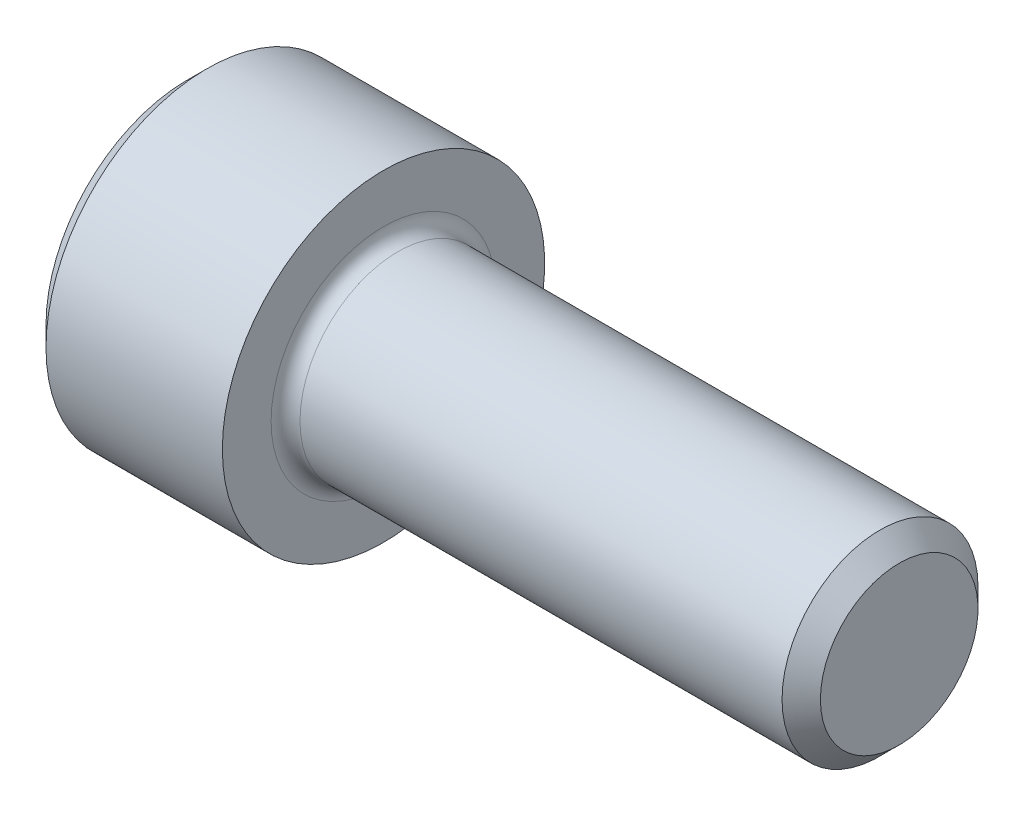
SolidWorks part; units mm, degrees
revolve "Base-Revolve" add sketch "BodySke" angle 360 about L6
sketch "BodySke" plane through (0, 0, 0) normal (0, 0, 1) x (1, 0, 0)
  line L0 (0, 0) -> (0, 3.4861)
  line L1 (0.4826, 3.9687) -> (4.826, 3.9687)
  line L2 (4.826, 3.9687) -> (4.826, 2.413)
  line L3 (4.826, 2.413) -> (17.0536, 2.413)
  line L4 (17.526, 1.9406) -> (17.526, 0)
  line L5 (17.526, 0) -> (0, 0)
  line L6 (-31.75, 0) -> (127, 0) construction
  line L7 (0, 3.4861) -> (0.4826, 3.9687)
  line L8 (17.526, 1.9406) -> (17.0536, 2.413)
  line L9 (0, -3.4862) -> (0.4826, -3.9688) construction
  line L10 (17.526, -1.9406) -> (17.0536, -2.413) construction
  line L11 (5.6185, 9.525) -> (5.6185, 3.175) construction
  line L12 (4.826, 9.525) -> (4.826, 3.175) construction
  line L13 (-20.574, 9.525) -> (-20.574, 3.175) construction
  dimension "Diameter" = 4.826
  dimension "Head_ht" = 4.826
  dimension "Length" = 12.7
  dimension "Body_ch_ang" = 45
  dimension "Head_dia" = 7.9375
  dimension "Head_ch_ang" = 45
  dimension "Head_side_ht" = 4.3434
  dimension "Minor_dia" = 3.8811
  dimension "Advance" = 0.7925
  dimension "Thread_nom" = 12.7
  dimension "Thread_length" = 38.1
cosmetic thread "ThreadCosmetic" parameters "Thread_length"=11.9075, "Thread_minor"=3.8811
material "Alloy Steel"
ref_plane "Plane1" through (0, 0, 0) normal (0, 0, 1) x (1, 0, 0)
ref_plane "Plane2" through (0, 0, 0) normal (0, 1, 0) x (1, 0, 0)
ref_plane "Plane3" through (0, 0, 0) normal (1, 0, 0) x (0, 0, -1)
fillet "Fillet1" radius 0.3556 1 edges at (4.826, 0, 2.413)
sketch "Sketch2" plane through (0, 0, 0) normal (0, 0, 1) x (1, 0, 0)
  line L0 (0, 1.985) -> (2.286, 1.985)
  line L1 (2.286, 1.985) -> (3.432, 0)
  line L2 (-31.75, 0) -> (127, 0) construction
  line L3 (3.432, 0) -> (0, 0)
  line L4 (0, 0) -> (0, 1.985)
  line L5 (0, 3.4861) -> (0, -3.4861) construction
  line L6 (0, 0) -> (47.625, 0) construction
  line L7 (4.826, -3.9687) -> (4.826, 3.9687) construction
  dimension "D1" = 1.985
  dimension "D2" = 60
revolve "Hex-PreBroach" cut sketch "Sketch2" angle 360 about L6
sketch "Sketch3" plane through (0, 0, 0) normal (-1, 0, 0) x (0, 0.5, 0.866)
  line L0 (1.146, 1.985) -> (-1.146, 1.985)
  line L1 (-1.146, 1.985) -> (-2.2921, 0)
  line L2 (1.146, 1.985) -> (2.2921, 0)
  line L3 (1.146, -1.985) -> (2.2921, 0)
  line L4 (1.146, -1.985) -> (-1.146, -1.985)
  line L5 (-1.146, -1.985) -> (-2.2921, 0)
  dimension "D1" = 1.985
  dimension "D2" = 1.985
  dimension "Hex_size" = 3.97
extrude "Hex" cut sketch "Sketch3" against normal blind 2.286
sketch "Sketch4" plane through (0, 0, 0) normal (-1, 0, 0) x (0, 0, 1)
  line L0 (0, 0) -> (2.3876, 0)
  line L1 (0, 0) -> (6.1484, 3.5498) construction
  line L2 (0, 0) -> (1.1938, 2.0677)
  line L3 (1.9883, 0.576) -> (2.2704, 0.7389)
  line L4 (1.493, 1.4339) -> (1.7751, 1.5968)
  arc A0 (1.9883, 0.576) -> (1.493, 1.4339) centre (0, 0) ccw
  arc A1 (2.3876, 0) -> (2.2704, 0.7389) centre (0, 0) ccw
  arc A2 (1.1938, 2.0677) -> (1.7751, 1.5968) centre (0, 0) cw
  dimension "D1" = 30
  dimension "D2" = 60
  dimension "Spline_p_dim" = 0.9906
  dimension "D3" = 0.4953
extrude "Spline" [suppressed] cut sketch "Sketch4" against normal blind 2.286
pattern_circular "CirPattern1" [suppressed] count 6 every 60 about axis through (-31.75, 0, 0) along (1, 0, 0)
sketch "Sketch5" plane through (0, 0, 0) normal (0, 0, 1) x (1, 0, 0)
  line L0 (-31.75, 0) -> (127, 0) construction
  line L2 (0, 3.4861) -> (0, -3.4861) construction
  circle A0 centre (1.651, 0) radius 0.5905
  dimension "Drilled_hole_dia" = 1.1811
  dimension "Drilled_hole_loc" = 1.651
extrude "Hole" [suppressed] cut sketch "Sketch5" against normal through all and the other way through all
pattern_circular "Drilled-4" [suppressed] count 2 every 60 about axis through (-31.75, 0, 0) along (1, 0, 0)
pattern_circular "Drilled-6" [suppressed] count 3 every 60 about axis through (-31.75, 0, 0) along (1, 0, 0)
sketch "ThdSchSke" plane through (0, 0, 0) normal (0, 0, 1) x (1, 0, 0)
  line L0 (5.6185, -1.9406) -> (5.2877, -2.413)
  line L1 (5.6185, -1.9406) -> (5.9493, -2.413)
  line L2 (5.9493, -2.413) -> (5.9493, -3.0163)
  line L3 (-3.175, 0) -> (5.1513, 0) construction
  line L5 (5.9493, -3.0163) -> (5.2877, -3.0163)
  line L6 (5.2877, -3.0163) -> (5.2877, -2.413)
  line L7 (0, 3.4861) -> (0, -3.4861) construction
  dimension "Thread_minor" = 3.8811
  dimension "Diameter" = 4.826
  dimension "Start" = 5.6185
revolve "ThreadSchematic" [suppressed] cut sketch "ThdSchSke" angle 360 about L3
pattern_linear "ThdSchPat" [suppressed]
equation "\"D2@Sketch3\" = \"Hex_size@Sketch3\" / 2"
equation "\"D1@Sketch3\" = \"Hex_size@Sketch3\" / 2"
equation "\"D1@Sketch2\" = \"Hex_size@Sketch3\" / 2"
equation "\"D3@Sketch4\" = \"Spline_p_dim@Sketch4\" / 2"
equation "\"Thread_minor@ThreadCosmetic\"  =  \"Minor_dia@BodySke\""
equation "\"D2@CirPattern1\" = 360 / \"Num_teeth@CirPattern1\""
equation "\"Wall_thickness@Sketch2\" = \"Head_ht@BodySke\" - \"Key_eng@Hex\""
equation "\"Thread_length@ThreadCosmetic\" = ((sgn( (\"Length@BodySke\" - \"Advance@BodySke\" ) - \"Thread_nom@BodySke\" )-1)*( (\"Length@BodySke\" - \"Advance@BodySke\" ) - \"Thread_nom@BodySke\" ))/-2+ \"Thread_nom@BodySke\""
equation "\"Thread_minor@ThdSchSke\" = \"Minor_dia@BodySke\""
equation "\"Diameter@ThdSchSke\" = \"Diameter@BodySke\""
equation "\"Overcut@ThdSchSke\" = \"Diameter@BodySke\" * 1.25"
equation "\"Start@ThdSchSke\" = \"Head_ht@BodySke\" + \"Length@BodySke\" - \"Thread_length@ThreadCosmetic\"  '---Non-countersunk---"
equation "\"Num_threads@ThdSchPat\" = int( \"Thread_length@ThreadCosmetic\" / \"Advance@BodySke\" + 0.999 )  + 1"
equation "\"Advance@ThdSchPat\" = \"Thread_length@ThreadCosmetic\" /  (\"Num_threads@ThdSchPat\" - 1) 'relax it"
equation "\"Num_threads@ThdSchPat\" = \"Num_threads@ThdSchPat\" - sgn( \"Num_threads@ThdSchPat\" - 1) '---chamfered tips only---"
